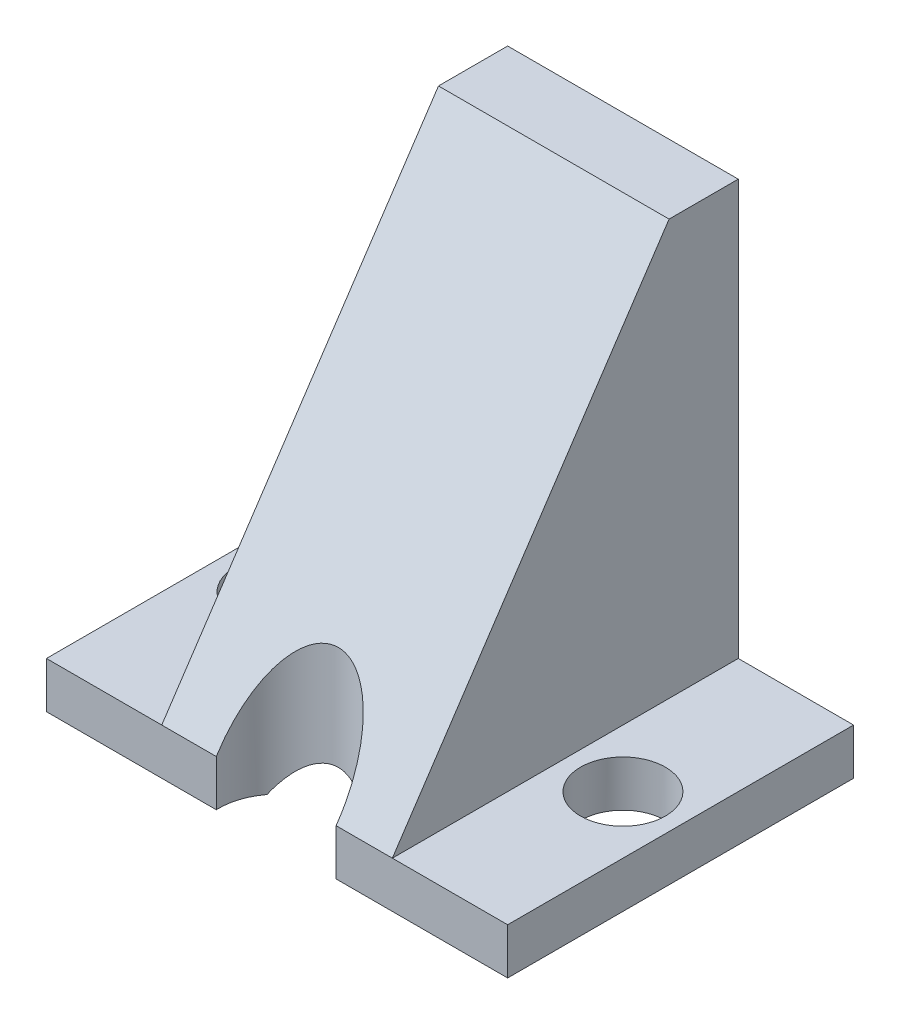
SolidWorks part; units mm, degrees
ref_plane "Front Plane" through (0, 0, 0) normal (0, 0, 1) x (1, 0, 0)
ref_plane "Top Plane" through (0, 0, 0) normal (0, 1, 0) x (1, 0, 0)
ref_plane "Right Plane" through (0, 0, 0) normal (1, 0, 0) x (0, 0, -1)
sketch "Sketch1" plane through (0, 0, 0) normal (0, 1, 0) x (1, 0, 0)
  line L1 (0, 0) -> (25.4, 0)
  line L2 (0, 0) -> (0, 19.05)
  line L3 (0, 19.05) -> (25.4, 19.05)
  line L4 (25.4, 0) -> (25.4, 19.05)
  dimension "D1" = 19.05
  dimension "D2" = 25.4
extrude "Boss-Extrude1" add sketch "Sketch1" along normal blind 25.4
chamfer "Chamfer1" distance 22.86 distance2 15.24 1 edges at (12.7, 25.4, 0)
sketch "Sketch2" plane through (0, 25.4, 0) normal (0, 1, 0) x (1, 0, 0)
  line L0 (25.4, 19.05) -> (0, 19.05) construction
  line L1 (19.05, 19.05) -> (25.4, 19.05)
  line L2 (19.05, 19.05) -> (19.05, -3.7392)
  line L3 (19.05, -3.7392) -> (25.4, -3.7392)
  line L4 (25.4, 19.05) -> (25.4, -3.7392)
  line L5 (25.4, 15.24) -> (25.4, 19.05) construction
  line L6 (0, 19.05) -> (6.35, 19.05)
  line L7 (0, 19.05) -> (0, -3.7392)
  line L8 (0, -3.7392) -> (6.35, -3.7392)
  line L9 (6.35, 19.05) -> (6.35, -3.7392)
  dimension "D1" = 6.35
  dimension "D2" = 6.35
  dimension "D3" = 0
extrude "Cut-Extrude1" cut sketch "Sketch2" against normal blind 22.86
ref_plane "Plane1" through (0, -0.9796, -1.4695) normal (0, 0.5547, 0.8321) x (1, 0, 0)
sketch "Sketch3" plane through (0, -0.9796, -1.4695) normal (0, 0.5547, 0.8321) x (1, 0, 0)
  line L0 (6.35, 2.1134) -> (6.35, 29.5877) construction
  line L1 (7.874, 34.3246) -> (17.526, 34.3246)
  line L2 (7.874, 34.3246) -> (7.874, -5.0291)
  line L3 (7.874, -5.0291) -> (17.526, -5.0291)
  line L4 (17.526, 34.3246) -> (17.526, -5.0291)
  dimension "D1" = 1.524
  dimension "D2" = 9.652
extrude "Cut-Extrude2" cut sketch "Sketch3" against normal blind 22.86
sketch "Sketch4" plane through (0, 2.54, 0) normal (0, 1, 0) x (1, 0, 0)
  line L0 (0, 19.05) -> (0, 0) construction
  line L1 (6.35, 19.05) -> (0, 19.05) construction
  line L2 (25.4, 19.05) -> (19.05, 19.05) construction
  line L3 (25.4, 0) -> (25.4, 19.05) construction
  circle A0 centre (3.175, 9.525) radius 2.3368
  circle A1 centre (22.225, 9.525) radius 2.3368
  dimension "D5" = 4.6736
  dimension "D6" = 4.6736
  dimension "D1" = 3.175
  dimension "D2" = 9.525
  dimension "D3" = 9.525
  dimension "D4" = 3.175
extrude "Cut-Extrude3" cut sketch "Sketch4" against normal blind 22.86
sketch "Sketch6" plane through (0, 0, 0) normal (0, -1, 0) x (1, 0, 0)
  circle A0 centre (12.6526, -0.1245) radius 3.302
extrude "Cut-Extrude5" cut sketch "Sketch6" against normal through all
